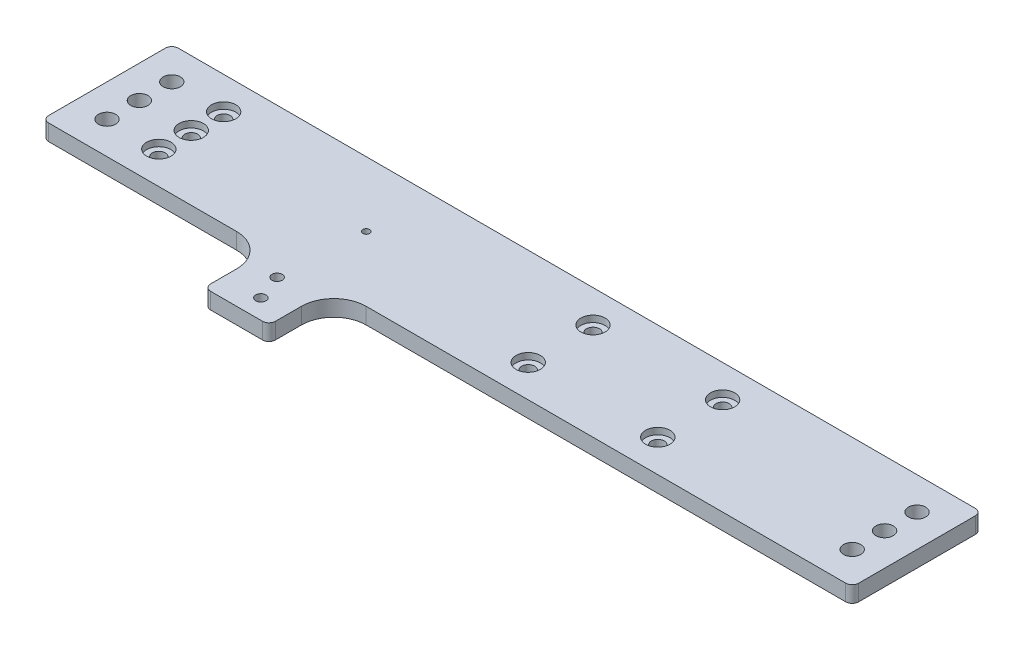
SolidWorks part; units mm, degrees
material "6061-T6 (SS)"
ref_plane "Front" through (0, 0, 0) normal (0, 0, 1) x (1, 0, 0)
ref_plane "Top" through (0, 0, 0) normal (0, 1, 0) x (1, 0, 0)
ref_plane "Right" through (0, 0, 0) normal (1, 0, 0) x (0, 0, -1)
sketch "Sketch1" plane through (0, 0, 0) normal (0, 1, 0) x (1, 0, 0)
  line L1 (-158.75, -25.4) -> (158.75, -25.4)
  line L2 (-158.75, -25.4) -> (-158.75, 25.4)
  line L3 (-158.75, 25.4) -> (158.75, 25.4)
  line L4 (158.75, -25.4) -> (158.75, 25.4)
  line L5 (-158.75, -25.4) -> (158.75, 25.4) construction
  line L6 (-158.75, 25.4) -> (158.75, -25.4) construction
  point P0 (0, 0)
  dimension "D1" = 50.8
  dimension "D2" = 317.5
extrude "Boss-Extrude1" add sketch "Sketch1" along normal blind 6.35
hole_wizard "CBORE for #10 Socket Head Cap Screw1" positions "Sketch2" profile "Sketch4" counterbore size "#10" standard "ANSI Inch" end condition through all
sketch "Sketch2" plane through (0, 6.35, 0) normal (0, 1, 0) x (1, 0, 0)
  line L2 (158.75, 25.4) -> (-158.75, 25.4) construction
  line L6 (-158.75, -25.4) -> (158.75, -25.4) construction
  line L8 (-158.75, 25.4) -> (-158.75, -25.4) construction
  line L12 (158.75, -25.4) -> (158.75, 25.4) construction
  line L15 (19.05, 12.7) -> (19.05, 25.4) construction
  line L17 (19.05, -12.7) -> (19.05, -25.4) construction
  line L18 (-125.73, -25.4) -> (-125.73, -12.7) construction
  line L20 (-125.73, 0) -> (-125.73, 12.7) construction
  line L21 (-125.73, 12.7) -> (-125.73, 25.4) construction
  line L22 (-125.73, 0) -> (-125.73, -12.7) construction
  point P64 (19.05, 12.7)
  point P66 (69.85, 12.7)
  point P68 (19.05, -12.7)
  point P70 (69.85, -12.7)
  point P92 (-125.73, 12.7)
  point P94 (-125.73, 0)
  point P102 (-125.73, -12.7)
  dimension "D2" = 50.8
  dimension "D3" = 25.4
  dimension "D4" = 88.9
  dimension "D5" = 33.02
sketch "Sketch4" plane through (-125.73, 6.35, 12.7) normal (1, 0, 0) x (0, 0, 1)
  line L0 (0, 0) -> (0, 6.35)
  line L1 (0, 6.35) -> (2.5527, 6.35)
  line L3 (2.5527, 6.35) -> (2.5527, 2.54)
  line L4 (2.5527, 2.54) -> (4.7625, 2.54)
  line L5 (4.7625, 2.54) -> (4.7625, 0)
  line L7 (4.7625, 0) -> (0, 0)
  line L11 (0, -6.35) -> (0, 107.95) construction
  dimension "Thru Hole Dia." = 5.1054
  dimension "Thru Hole Depth" = 6.35
  dimension "C'Bore Dia." = 9.525
  dimension "C'Bore Depth" = 2.54
sketch "Sketch7" plane through (0, 0, 0) normal (0, -1, 0) x (1, 0, 0)
  line L0 (-146.05, 25.4) -> (-146.05, 12.7) construction
  line L1 (-158.75, 25.4) -> (158.75, 25.4) construction
  line L2 (-146.05, 12.7) -> (-146.05, 0) construction
  line L3 (-146.05, 0) -> (-146.05, -12.7) construction
  line L4 (-146.05, -12.7) -> (-146.05, -25.4) construction
  line L5 (158.75, -25.4) -> (-158.75, -25.4) construction
  line L7 (-158.75, -25.4) -> (-158.75, 25.4) construction
  line L8 (146.05, 25.4) -> (146.05, 12.7) construction
  line L9 (146.05, 12.7) -> (146.05, 0) construction
  line L10 (146.05, 0) -> (146.05, -12.7) construction
  line L11 (146.05, -12.7) -> (146.05, -25.4) construction
  line L13 (158.75, 25.4) -> (158.75, -25.4) construction
  point P0 (-146.05, 12.7)
  point P2 (-146.05, 0)
  point P4 (-146.05, -12.7)
  point P6 (146.05, 12.7)
  point P8 (146.05, 0)
  point P10 (146.05, -12.7)
  dimension "D1" = 12.7
  dimension "D2" = 12.7
hole_wizard "1/4 Clearance Hole2" positions "Sketch7" profile "Sketch6" hole size "1/4" standard "ANSI Inch" end condition through all
sketch "Sketch6" plane through (-146.05, 0, 12.7) normal (1, 0, 0) x (0, 0, -1)
  line L0 (0, 0) -> (0, 6.35)
  line L1 (0, 6.35) -> (3.3782, 6.35)
  line L2 (3.3782, 6.35) -> (3.3782, 0)
  line L5 (3.3782, 0) -> (0, 0)
  line L11 (0, -6.35) -> (0, 107.95) construction
  dimension "Thru Hole Dia." = 6.7564
  dimension "Thru Hole Depth" = 6.35
sketch "Sketch10" plane through (0, 0, 0) normal (0, -1, 0) x (-1, 0, 0)
  line L0 (158.75, 25.4) -> (158.75, -25.4) construction
  point P0 (57.15, 0)
  dimension "D1" = 101.6
hole_wizard "#6-32 Tapped Hole1" positions "Sketch10" profile "Sketch9" tap size "#6-32" standard "ANSI Inch" end condition through all
sketch "Sketch9" plane through (-57.15, 0, 0) normal (1, 0, 0) x (0, 0, -1)
  line L0 (0, 0) -> (0, 6.35)
  line L1 (0, 6.35) -> (1.3525, 6.35)
  line L2 (1.3525, 6.35) -> (1.3525, 0)
  line L5 (1.3525, 0) -> (0, 0)
  line L11 (0, -6.35) -> (0, 107.95) construction
  dimension "Thru Tap Drill Dia." = 2.7051
  dimension "Thru Tap Drill Depth" = 6.35
cosmetic thread "Hole Thread1" parameters "D2"=3.5052
sketch "Sketch11" plane through (0, 0, 0) normal (0, -1, 0) x (1, 0, 0)
  line L0 (158.75, -25.4) -> (-158.75, -25.4) construction
  line L1 (-70.0118, -25.4) -> (-48.1024, -25.4)
  line L2 (-70.0118, -25.4) -> (-70.0118, -45.81)
  line L3 (-70.0118, -45.81) -> (-48.1024, -45.81)
  line L4 (-48.1024, -25.4) -> (-48.1024, -45.81)
extrude "Boss-Extrude2" [suppressed] add sketch "Sketch11" against normal up to surface (6.35 mm away)
sketch "Sketch12" plane through (0, 6.35, 0) normal (0, 1, 0) x (1, 0, 0)
  line L0 (-158.75, -25.4) -> (158.75, -25.4) construction
  line L1 (-69.85, -25.4) -> (-44.45, -25.4)
  line L2 (-69.85, -25.4) -> (-69.85, -50.8)
  line L3 (-69.85, -50.8) -> (-44.45, -50.8)
  line L4 (-44.45, -25.4) -> (-44.45, -50.8)
  line L5 (-158.75, 25.4) -> (-158.75, -25.4) construction
  dimension "D1" = 88.9
  dimension "D2" = 25.4
  dimension "D3" = 25.4
extrude "Boss-Extrude3" add sketch "Sketch12" against normal up to surface (6.35 mm away) up to face at (-57.15, 0, -1.3526)
sketch "Sketch15" plane through (0, 0, 0) normal (0, -1, 0) x (-1, 0, 0)
  point P0 (55.245, -43.18)
  point P3 (59.055, -33.02)
hole_wizard "#10-32 Tapped Hole1" positions "Sketch15" profile "Sketch14" tap size "#10-32" standard "ANSI Inch" end condition through all
sketch "Sketch14" plane through (-55.245, 0, 43.18) normal (1, 0, 0) x (0, 0, -1)
  line L0 (0, 0) -> (0, 6.35)
  line L1 (0, 6.35) -> (2.0193, 6.35)
  line L2 (2.0193, 6.35) -> (2.0193, 0)
  line L5 (2.0193, 0) -> (0, 0)
  line L11 (0, -6.35) -> (0, 107.95) construction
  dimension "Thru Tap Drill Dia." = 4.0386
  dimension "Thru Tap Drill Depth" = 6.35
fillet "Fillet1" radius 12.7 2 edges at (-69.85, 3.175, 25.4) (-44.45, 3.175, 25.4)
fillet "Fillet2" radius 2.54 6 edges at (158.75, 3.175, 25.4) (158.75, 3.175, -25.4) (-158.75, 3.175, -25.4) (-158.75, 3.175, 25.4) (-69.85, 3.175, 50.8) (-44.45, 3.175, 50.8)
